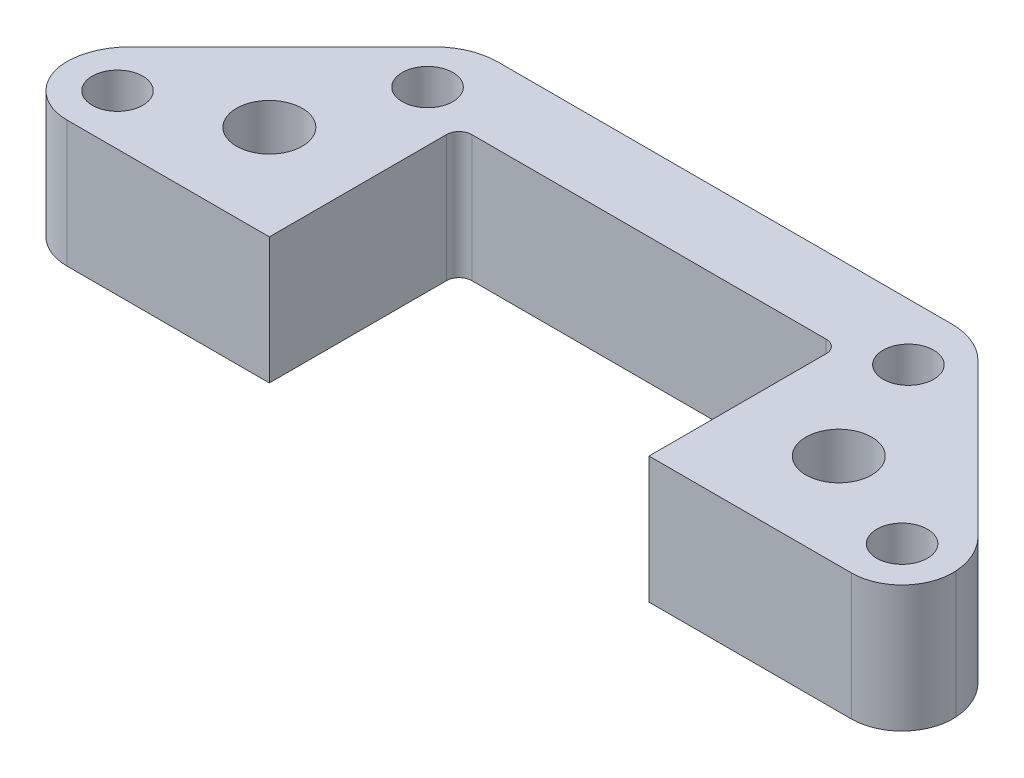
SolidWorks part; units mm, degrees
ref_plane "Plan de face" through (0, 0, 0) normal (0, 0, 1) x (1, 0, 0)
ref_plane "Plan de dessus" through (0, 0, 0) normal (0, 1, 0) x (1, 0, 0)
ref_plane "Plan de droite" through (0, 0, 0) normal (1, 0, 0) x (0, 0, -1)
sketch "Esquisse1" plane through (0, 0, 0) normal (0, 1, 0) x (1, 0, 0)
  line L0 (-30, 15) -> (-15, 0) construction
  line L1 (-30, 0) -> (-15, 0) construction
  line L2 (-30, 0) -> (-30, 15) construction
  line L3 (-30, 15) -> (-15, 15) construction
  line L4 (-15, 0) -> (-15, 15) construction
  line L5 (15, 0) -> (30, 0) construction
  line L6 (15, 0) -> (15, 15) construction
  line L7 (15, 15) -> (30, 15) construction
  line L8 (30, 0) -> (30, 15) construction
  line L9 (15, 0) -> (30, 15) construction
  line L10 (-15, 0) -> (15, 0) construction
  line L11 (-20, 21) -> (20, 21)
  line L12 (-14, 15) -> (14, 15)
  line L13 (0, 21) -> (0, 0) construction
  line L20 (-14, 15) -> (-15, 14)
  line L21 (-15, 14) -> (-15, 0)
  line L22 (14, 15) -> (15, 14)
  line L23 (15, 14) -> (15, 0)
  line L24 (-15, 14) -> (15, 14) construction
  line L29 (-15, 0) -> (-35, 0)
  line L30 (15, 0) -> (35, 0)
  line L31 (-20, 21) -> (-35, 6)
  line L32 (-35, 6) -> (-35, 0)
  line L33 (20, 21) -> (35, 6)
  line L34 (35, 6) -> (35, 0)
  circle A0 centre (-22.5, 7.5) radius 7.5 construction
  circle A1 centre (22.5, 7.5) radius 7.5 construction
  circle A2 centre (-22.5, 7.5) radius 2.6
  circle A3 centre (22.5, 7.5) radius 2.6
  point P8 (0, 0)
  point P21 (0, 15)
  dimension "D3" = 5.2
  dimension "D1" = 30
  dimension "D2" = 15
  dimension "D4" = 6
  dimension "D5" = 1
  dimension "D6" = 28
  dimension "D7" = 20
  dimension "D8" = 6
  dimension "D9" = 40
extrude "Boss.-Extru.1" add sketch "Esquisse1" along normal blind 10
sketch "Esquisse7" plane through (0, 0, 0) normal (0, -1, 0) x (1, 0, 0)
  line L0 (0, -21) -> (0, 12.4029) construction
  line L1 (20, -21) -> (-20, -21) construction
  circle A0 centre (22.5, -7.5) radius 5.1
  circle A1 centre (-22.5, -7.5) radius 5.1
  dimension "D1" = 10.2
extrude "Enlèv. mat.-Extru.4" cut sketch "Esquisse7" against normal blind 5.4
sketch "Esquisse4" plane through (0, 0, 0) normal (0, -1, 0) x (1, 0, 0)
  line L0 (19, -16.5) -> (-19, -16.5) construction
  line L1 (0, -16.5) -> (0, 0) construction
  line L2 (31, -4) -> (-31, -4) construction
  circle A0 centre (19, -16.5) radius 2
  circle A1 centre (-19, -16.5) radius 2
  circle A2 centre (-31, -4) radius 2
  circle A3 centre (31, -4) radius 2
  point P10 (0, -4)
  dimension "D3" = 4
  dimension "D4" = 62
  dimension "D1" = 16.5
  dimension "D2" = 38
  dimension "D5" = 4
extrude "Enlèv. mat.-Extru.2" cut sketch "Esquisse4" against normal up to surface (10 mm away) up to face at (-22.5, 10, -4.9)
sketch "Esquisse5" plane through (0, 10, 0) normal (0, 1, 0) x (1, 0, 0)
  line L0 (15, 14) -> (14, 14)
  line L1 (14, 14) -> (14, 15)
  line L2 (0, 0) -> (0, 21) construction
  line L3 (-30.9975, 0) -> (30.9975, 0) construction
  line L4 (20, 21) -> (-20, 21) construction
  line L5 (-14, 14) -> (-14, 15)
  line L6 (-15, 14) -> (-14, 14)
  arc A0 (15, 14) -> (14, 15) centre (14, 14) ccw
  arc A1 (-15, 14) -> (-14, 15) centre (-14, 14) cw
extrude "Enlèv. mat.-Extru.3" cut sketch "Esquisse5" against normal through all
fillet "Congé1" radius 5 4 edges at (35, 5, -6) (20, 5, -21) (-35, 5, -6) (-20, 5, -21)
fillet "Congé2" radius 4 2 edges at (35, 5, 0) (-35, 5, 0)
